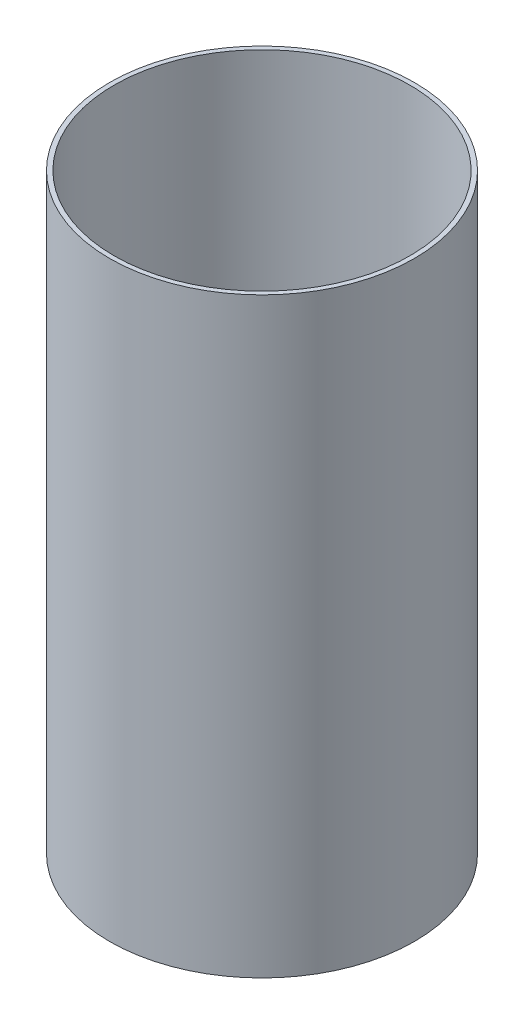
SolidWorks part; units mm, degrees
material "C-Glass Fiber"
ref_plane "Front Plane" through (0, 0, 0) normal (0, 0, 1) x (1, 0, 0)
ref_plane "Top Plane" through (0, 0, 0) normal (0, 1, 0) x (1, 0, 0)
ref_plane "Right Plane" through (0, 0, 0) normal (1, 0, 0) x (0, 0, -1)
sketch "Sketch1" plane through (0, 0, 0) normal (0, 1, 0) x (1, 0, 0)
  circle A0 centre (0, 0) radius 63.5
  circle A1 centre (0, 0) radius 65.4431
  dimension "D1" = 127
  dimension "D2" = 130.8862
extrude "Boss-Extrude2" add sketch "Sketch1" along normal blind 254
